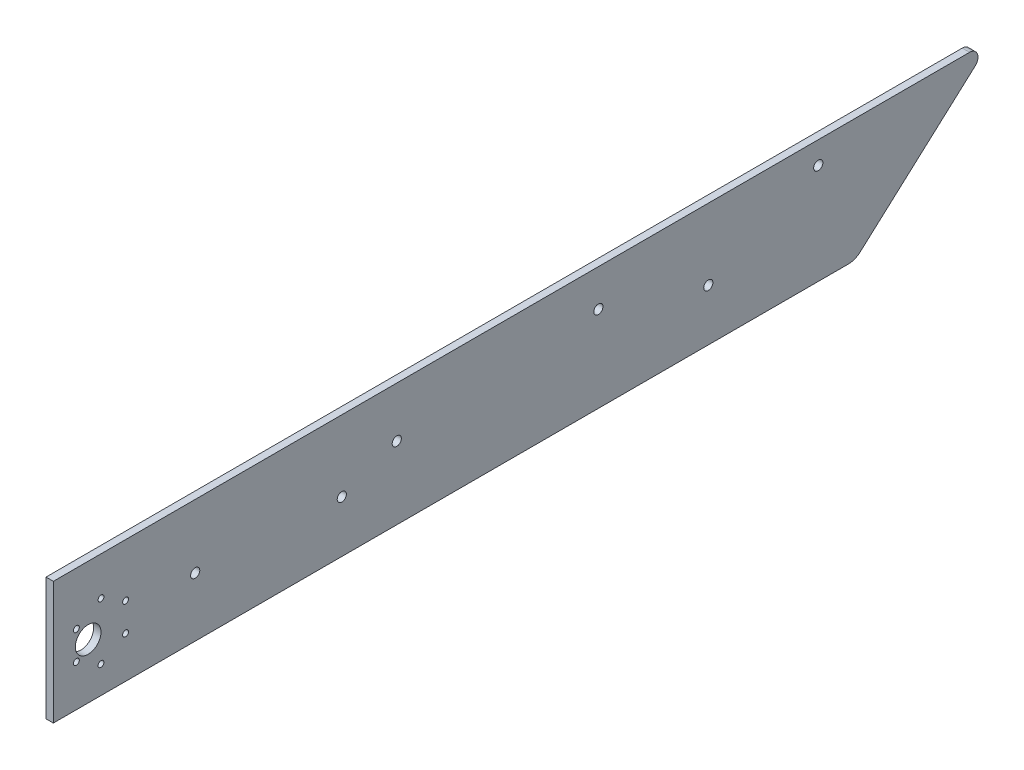
SolidWorks part; units mm, degrees
ref_plane "前视基准面" through (0, 0, 0) normal (0, 0, 1) x (1, 0, 0)
ref_plane "上视基准面" through (0, 0, 0) normal (0, 1, 0) x (1, 0, 0)
ref_plane "右视基准面" through (0, 0, 0) normal (1, 0, 0) x (0, 0, -1)
sketch "草图1" plane through (0, 0, 0) normal (-1, 0, 0) x (0, 0, 1)
  line L0 (-207.2522, -7.4046) -> (226.4067, -7.4046)
  line L160 (226.4067, 59.5954) -> (226.4067, -7.4046)
  line L161 (226.4067, 59.5954) -> (-273.5933, 59.5954)
  line L162 (-276.6521, 51.627) -> (-213.9436, -4.8361)
  arc A0 (-213.9436, -4.8361) -> (-207.2522, -7.4046) centre (-207.2522, 2.5954) ccw
  circle A4 centre (-191.0077, 47.4434) radius 2.5
  circle A5 centre (68.9923, 20.8287) radius 2.5
  circle A7 centre (38.9923, 32.1453) radius 2.5
  circle A11 centre (-131.0077, 20.8287) radius 2.5
  circle A12 centre (207.4067, 22.6023) radius 7
  circle A13 centre (148.9923, 24.8287) radius 2.5
  circle A14 centre (-71.0077, 39.4618) radius 2.5
  circle A28 centre (213.8301, 30.7569) radius 1.6
  circle A29 centre (200.4067, 38.5069) radius 1.6
  circle A30 centre (186.9833, 30.7569) radius 1.6
  circle A31 centre (186.9833, 15.2569) radius 1.6
  circle A32 centre (200.4067, 7.5069) radius 1.6
  circle A33 centre (213.8301, 15.2569) radius 1.6
  arc A525 (-273.5933, 59.5954) -> (-276.6521, 51.627) centre (-273.5933, 55.0241) ccw
  point P0 (-150, 0)
  point P1 (135, 0)
  point P9 (-344.9533, 138.7825)
  point P10 (187.1329, 101.1747)
  point P11 (165.9429, -19)
  point P12 (-156.9154, -19)
  dimension "D7" = 19
  dimension "D8" = 80
  dimension "D9" = 30
  dimension "D10" = 110
  dimension "D11" = 60
  dimension "D12" = 60
  dimension "D6" = 36.9931
  dimension "D2" = 10
  dimension "D1" = 500
  dimension "D3" = 138
extrude "凸台-拉伸1" add sketch "草图1" along normal blind 4
